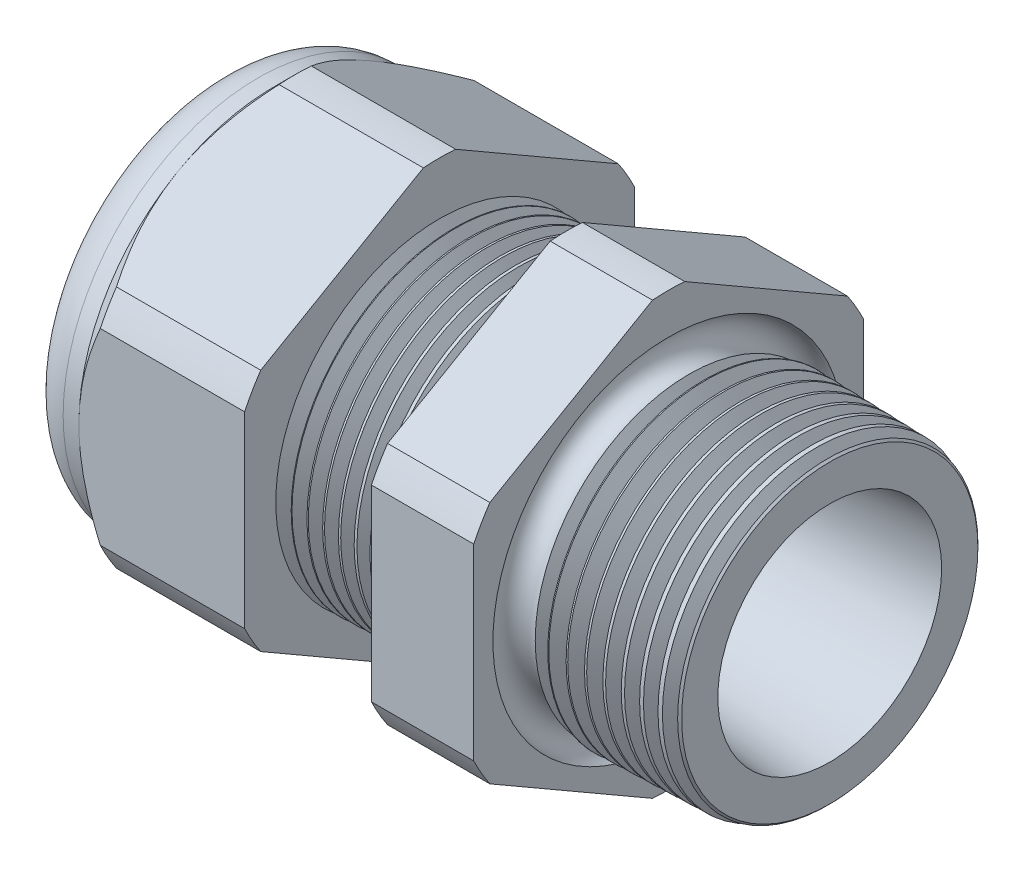
SolidWorks part; units mm, degrees
ref_plane "Front Plane" through (0, 0, 0) normal (0, 0, 1) x (1, 0, 0)
ref_plane "Top Plane" through (0, 0, 0) normal (0, 1, 0) x (1, 0, 0)
ref_plane "Right Plane" through (0, 0, 0) normal (1, 0, 0) x (0, 0, -1)
sketch "Sketch10" plane through (0, 0, 0) normal (0, 0, 1) x (1, 0, 0)
  line L0 (0, 0) -> (-115.3565, 0) construction
  line L1 (-29.972, 3.937) -> (-19.072, 3.937)
  line L2 (0, 5.4696) -> (0, 7.5016)
  line L3 (-7.874, 7.7078) -> (0, 7.5016)
  line L4 (-7.874, 19.05) -> (-7.874, 7.7078)
  line L5 (-7.874, 19.05) -> (-12.874, 19.05)
  line L6 (-12.874, 19.05) -> (-12.874, 7.8387)
  line L7 (-19.072, 8.001) -> (-12.874, 7.8387)
  line L8 (-19.072, 8.001) -> (-19.072, 19.05)
  line L9 (-19.072, 19.05) -> (-27.172, 19.05)
  line L10 (-27.172, 19.05) -> (-27.172, 9.525)
  line L11 (-27.172, 9.525) -> (-29.972, 9.525)
  line L12 (-29.972, 9.525) -> (-29.972, 3.937)
  line L13 (-19.072, 3.937) -> (0, 5.4696)
  dimension "D1" = 29.972
  dimension "D2" = 7.874
  dimension "D3" = 1.5
  dimension "D4" = 2.032
  dimension "A" = 16.002
  dimension "D6" = 19.05
  dimension "D8" = 38.1
  dimension "D9" = 2.8
  dimension "D10" = 8.1
  dimension "D11" = 5
  dimension "D" = 7.874
revolve "Revolve2" add sketch "Sketch10" angle 360 about L0
sketch "Sketch12" plane through (-27.172, 0, 0) normal (-1, 0, 0) x (0, 0, 1)
  line L1 (-0.7885, 10.5433) -> (-8.7365, 5.9545)
  line L2 (-9.525, 4.5888) -> (-9.525, -4.5888)
  line L3 (-8.7365, -5.9545) -> (-0.7885, -10.5433)
  line L4 (0.7885, -10.5433) -> (8.7365, -5.9545)
  line L5 (9.525, -4.5888) -> (9.525, 4.5888)
  line L6 (8.7365, 5.9545) -> (0.7885, 10.5433)
  circle A0 centre (0, 0) radius 9.525 construction
  arc A1 (0.7885, 10.5433) -> (-0.7885, 10.5433) centre (0, 0) ccw
  arc A2 (-8.7365, 5.9545) -> (-9.525, 4.5888) centre (0, 0) ccw
  arc A3 (-9.525, -4.5888) -> (-8.7365, -5.9545) centre (0, 0) ccw
  arc A4 (-0.7885, -10.5433) -> (0.7885, -10.5433) centre (0, 0) ccw
  arc A5 (8.7365, -5.9545) -> (9.525, -4.5888) centre (0, 0) ccw
  arc A6 (9.525, 4.5888) -> (8.7365, 5.9545) centre (0, 0) ccw
  dimension "D2" = 21.1455
  dimension "D1" = 19.05
extrude "Cut-Extrude2" cut sketch "Sketch12" against normal through all flip side to cut
fillet "Fillet4" radius 2.032 1 edges at (-29.972, 0, -9.525)
sketch "Sketch19" plane through (-27.172, 0, 0) normal (-1, 0, 0) x (0, 0, 1)
  line L0 (9.525, 0) -> (9.525, 4.5888) construction
  circle A0 centre (0, 0) radius 9.525
extrude "Cut-Extrude3" cut sketch "Sketch19" against normal blind 2 draft 45 flip side to cut
chamfer "Chamfer1" distance 0.254 angle 45 1 edges at (0, 0, -7.5016)
sketch "Sketch21" plane through (-29.972, 0, 0) normal (-1, 0, 0) x (0, 0, 1)
  circle A0 centre (0, 0) radius 3.937
  circle A2 centre (0, 0) radius 3.937 construction
extrude "plug" add sketch "Sketch21" against normal blind 3.81 separate body
sketch "Sketch22" plane through (-29.972, 0, 0) normal (-1, 0, 0) x (0, 0, 1)
  circle A0 centre (0, 0) radius 3.683
  circle A1 centre (0, 0) radius 3.937 construction
  dimension "D1" = 0.254
extrude "Cut-Extrude4" cut sketch "Sketch22" against normal blind 0.508
sketch "Sketch27" plane through (-29.464, 0, 0) normal (-1, 0, 0) x (0, 0, 1)
  line L0 (-4.3624, 0) -> (4.3624, 0) construction
  circle A0 centre (-2.918, 0) radius 0.762
  circle A1 centre (0, 0) radius 3.683 construction
  dimension "D1" = 0.003
  dimension "holedia" = 1.524
extrude "plugholes" cut sketch "Sketch27" against normal through all
pattern_circular "CirPattern1" count 9 over 360 about axis through (0, 0, 0) along (1, 0, 0) of "plugholes"
sketch "Sketch28" plane through (-29.464, 0, 0) normal (-1, 0, 0) x (0, 0, 1)
  circle A0 centre (0, 0) radius 0.762
  dimension "midholedia" = 1.524
extrude "midhole" cut sketch "Sketch28" against normal through all
sketch "Sketch29" plane through (0, 0, 0) normal (0, 0, 1) x (1, 0, 0)
  line L0 (-19.072, 8.001) -> (-18.339, 7.9818)
  line L1 (-12.874, 7.8387) -> (-19.072, 8.001) construction
  line L2 (-18.339, 7.9818) -> (-18.7221, 7.3566)
  line L3 (-18.7221, 7.3566) -> (-19.072, 8.001)
  dimension "D1" = 60
  dimension "D2" = 60
  dimension "D3" = 0.635
revolve "Cut-Revolve1" cut sketch "Sketch29" angle 360 about axis through (0, 0, 0) along (-1, 0, 0)
pattern_linear "LPattern1" count 8 spacing 0.762 along (1, 0, 0) of "Cut-Revolve1"
sketch "Sketch30" plane through (0, 0, 0) normal (0, 0, 1) x (1, 0, 0)
  line L0 (-7.874, 7.7078) -> (-6.9944, 7.6847)
  line L1 (-7.874, 10.5433) -> (-7.874, 5.9545) construction
  line L2 (-0.2539, 7.5082) -> (-7.874, 7.7078) construction
  line L3 (-6.9944, 7.6847) -> (-7.4542, 6.9345)
  line L4 (-7.4542, 6.9345) -> (-7.874, 7.7078)
  dimension "D1" = 60
  dimension "D2" = 60
  dimension "D3" = 0.762
revolve "Cut-Revolve2" cut sketch "Sketch30" angle 360 about axis through (0, 0, 0) along (-1, 0, 0)
pattern_linear "LPattern2" count 9 spacing 0.889 along (1, 0, 0) of "Cut-Revolve2"
sketch "Sketch31" [suppressed] plane through (-38.354, 0, 0) normal (-1, 0, 0) x (0, 0, 1)
  line L0 (-1.905, 1.905) -> (1.905, 1.905)
  line L1 (-1.905, -1.905) -> (1.905, -1.905)
  circle A0 centre (0, 0) radius 1.905 construction
  arc A1 (-1.905, 1.905) -> (-1.905, -1.905) centre (-1.905, 0) ccw
  arc A2 (1.905, 1.905) -> (1.905, -1.905) centre (1.905, 0) cw
extrude "Cut-Extrude5" [suppressed] cut sketch "Sketch31" against normal through all
sketch "Sketch32" plane through (0, 0, 0) normal (0, 0, 1) x (1, 0, 0)
  line L0 (-7.874, 10.5433) -> (-7.874, 5.9545) construction
  circle A0 centre (-7.747, 7.7078) radius 0.889
  dimension "D2" = 1.778
  dimension "D1" = 0.127
revolve "Cut-Revolve3" cut sketch "Sketch32" angle 360 about axis through (0, 0, 0) along (-1, 0, 0)
